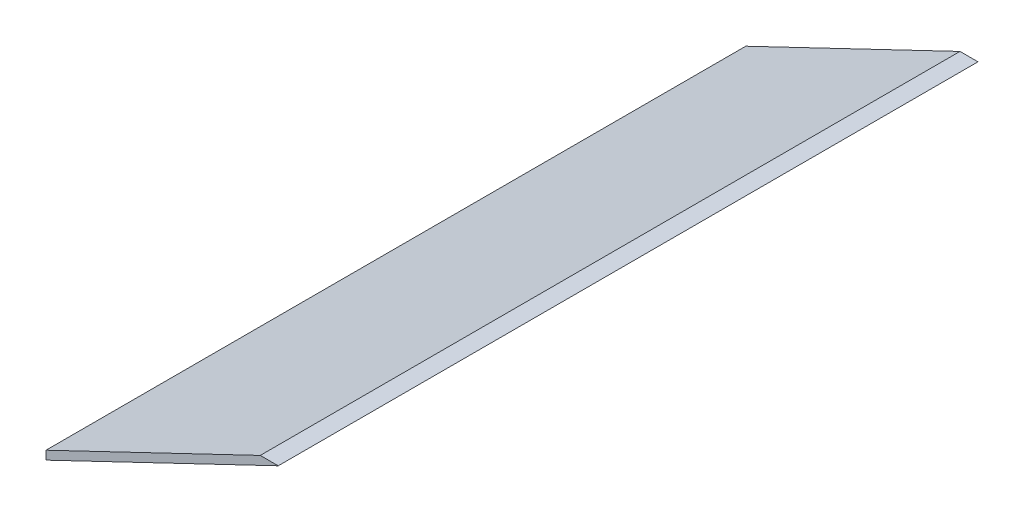
SolidWorks part; units mm, degrees
ref_plane "Ebene vorne" through (0, 0, 0) normal (0, 0, 1) x (1, 0, 0)
ref_plane "Ebene oben" through (0, 0, 0) normal (0, 1, 0) x (1, 0, 0)
ref_plane "Ebene rechts" through (0, 0, 0) normal (1, 0, 0) x (0, 0, -1)
sketch "Skizze1" plane through (0, 0, 0) normal (0, 0, 1) x (1, 0, 0)
  line L0 (97.5, 188.0437) -> (97.5, 182.5)
  line L1 (235.2816, 254.0237) -> (246.8583, 254.0237)
  line L30 (97.5, 188.0437) -> (235.2816, 254.0237)
  line L31 (97.5, 182.5) -> (246.8583, 254.0237)
extrude "Aufsatz-Linear austragen1" add sketch "Skizze1" along normal blind 450
